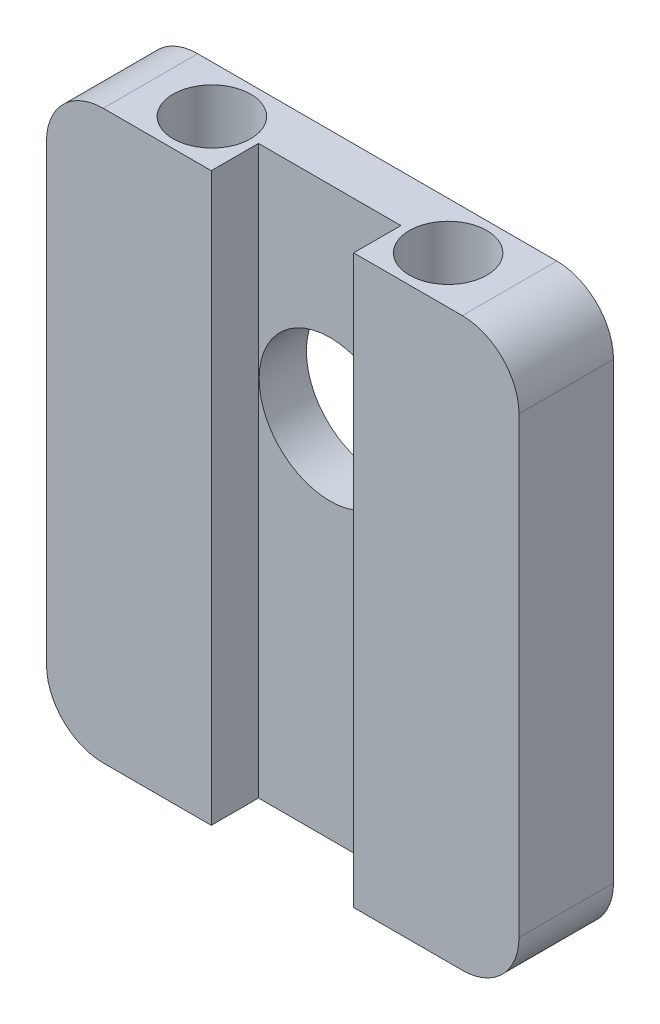
SolidWorks part; units mm, degrees
ref_plane "Front Plane" through (0, 0, 0) normal (0, 0, 1) x (1, 0, 0)
ref_plane "Top Plane" through (0, 0, 0) normal (0, 1, 0) x (1, 0, 0)
ref_plane "Right Plane" through (0, 0, 0) normal (1, 0, 0) x (0, 0, -1)
sketch "Sketch4" plane through (0, 0, 0) normal (0, 1, 0) x (1, 0, 0)
  line L1 (0, 0) -> (63.5, 0)
  line L2 (0, 0) -> (0, 12.7)
  line L3 (0, 12.7) -> (63.5, 12.7)
  line L4 (63.5, 0) -> (63.5, 12.7)
  line L5 (0, 0) -> (63.5, 12.7) construction
  line L6 (0, 12.7) -> (63.5, 0) construction
  point P5 (31.75, 6.35)
extrude "Boss-Extrude1" add sketch "Sketch4" along normal blind 76.2
sketch "Sketch5" plane through (0, 76.2, 0) normal (0, 1, 0) x (1, 0, 0)
  line L0 (31.75, 12.7) -> (0, 12.7) construction
  line L1 (63.5, 12.7) -> (0, 12.7) construction
  line L2 (31.75, 12.7) -> (63.5, 12.7) construction
  circle A2 centre (47.625, 6.35) radius 5.207
  circle A4 centre (15.875, 6.35) radius 5.207
extrude "Cut-Extrude1" cut sketch "Sketch5" against normal blind 69.85
sketch "Sketch7" plane through (0, 76.2, 0) normal (0, 1, 0) x (1, 0, 0)
  line L0 (21.082, 6.35) -> (22.1412, 6.35) construction
  line L1 (42.418, 6.35) -> (41.275, 6.35) construction
  line L2 (0, 0) -> (63.5, 0) construction
  line L3 (22.1412, 0) -> (41.275, 0)
  line L4 (22.1412, 0) -> (22.1412, 6.35)
  line L5 (22.1412, 6.35) -> (41.275, 6.35)
  line L6 (41.275, 0) -> (41.275, 6.35)
  line L7 (22.1412, 0) -> (41.275, 6.35) construction
  line L8 (22.1412, 6.35) -> (41.275, 0) construction
  circle A1 centre (15.875, 6.35) radius 5.207 construction
  circle A2 centre (47.625, 6.35) radius 5.207 construction
  circle A3 centre (47.625, 6.35) radius 5.207 construction
  point P17 (31.7081, 3.175)
extrude "Cut-Extrude2" cut sketch "Sketch7" against normal through all
ref_plane "Plane1" through (22.1412, 76.2, -6.35) normal (-1, 0, 0) x (0, 0, 1)
sketch "Sketch9" plane through (0, 0, -12.7) normal (0, 0, -1) x (-1, 0, 0)
  line L0 (-31.75, 76.2) -> (-31.75, 6.35) construction
  line L1 (-63.5, 76.2) -> (0, 76.2) construction
  line L2 (-35.1924, 6.35) -> (-35.1924, 13.97) construction
  line L3 (-33.3682, 6.35) -> (-33.3682, 36.83) construction
  circle A1 centre (-31.75, 48.895) radius 9.525
extrude "Cut-Extrude3" cut sketch "Sketch9" against normal through all
fillet "Fillet2" radius 7.62 4 edges at (0, 0, -6.35) (63.5, 0, -6.35) (0, 76.2, -6.35) (63.5, 76.2, -6.35)
